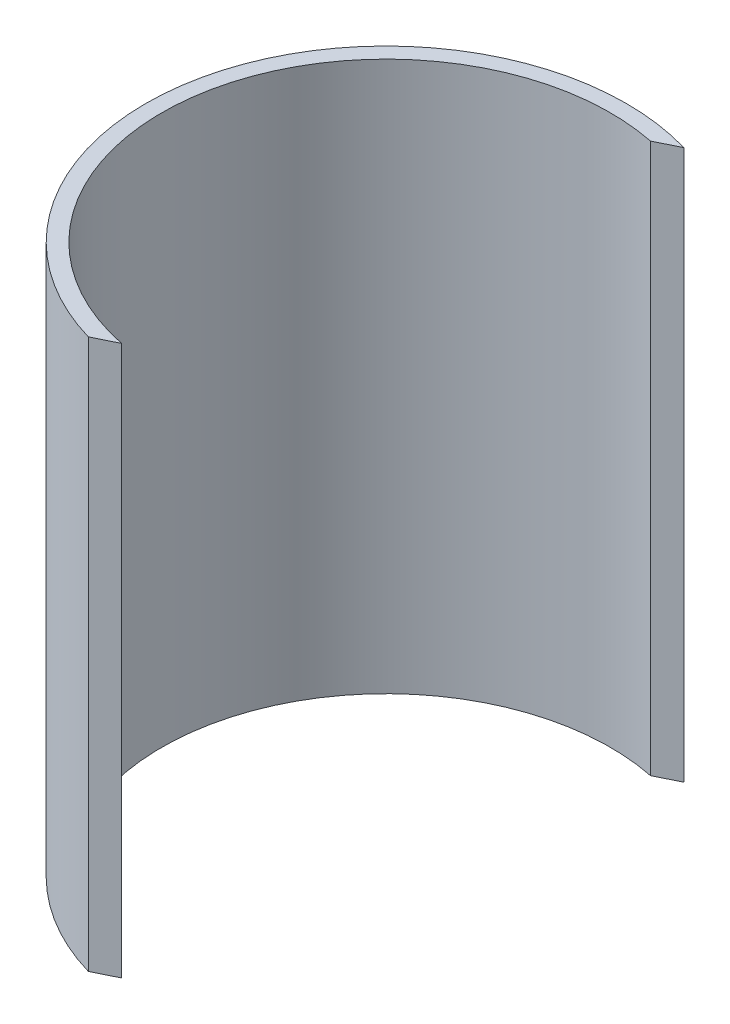
SolidWorks part; units mm, degrees
ref_plane "Alzado" through (0, 0, 0) normal (0, 0, 1) x (1, 0, 0)
ref_plane "Planta" through (0, 0, 0) normal (0, 1, 0) x (1, 0, 0)
ref_plane "Vista lateral" through (0, 0, 0) normal (1, 0, 0) x (0, 0, -1)
sketch "Croquis2" plane through (0, 0, 0) normal (0, 1, 0) x (1, 0, 0)
  line L0 (7.7322, 26.67) -> (5.1538, 25.4)
  line L1 (-7.7322, -26.67) -> (-5.1538, -25.4)
  arc A0 (-5.1538, -25.4) -> (5.1538, 25.4) centre (0, 0) cw
  arc A1 (-7.7322, -26.67) -> (7.7322, 26.67) centre (0, 0) cw
  dimension "D1" = 50.8
  dimension "D2" = 53.34
extrude "Saliente-Extruir4" add sketch "Croquis2" along normal blind 63.5
sketch3d "Croquis3D1" plane through (0, 0, 0) normal (0, 0, 1) x (1, 0, 0)
